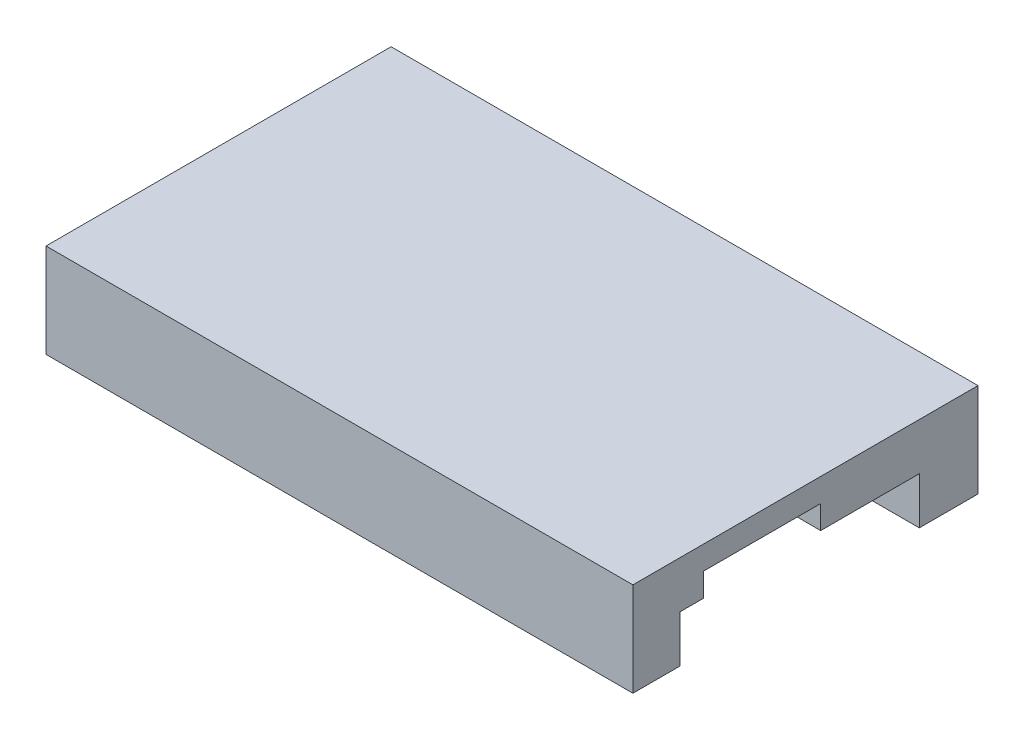
SolidWorks part; units mm, degrees
ref_plane "Front Plane" through (0, 0, 0) normal (0, 0, 1) x (1, 0, 0)
ref_plane "Top Plane" through (0, 0, 0) normal (0, 1, 0) x (1, 0, 0)
ref_plane "Right Plane" through (0, 0, 0) normal (1, 0, 0) x (0, 0, -1)
sketch "Sketch1" plane through (0, 0, 0) normal (0, 1, 0) x (1, 0, 0)
  line L1 (-42.4855, 20.9565) -> (-17.4855, 20.9565)
  line L2 (-42.4855, 20.9565) -> (-42.4855, 6.2565)
  line L3 (-42.4855, 6.2565) -> (-17.4855, 6.2565)
  line L4 (-17.4855, 20.9565) -> (-17.4855, 6.2565)
  dimension "D1" = 25
  dimension "D2" = 14.7
extrude "Boss-Extrude1" add sketch "Sketch1" along normal blind 1
sketch "Sketch2" plane through (0, 1, 0) normal (0, 1, 0) x (1, 0, 0)
  line L0 (-17.4855, 20.9565) -> (-42.4855, 20.9565) construction
  line L1 (-42.4855, 18.2565) -> (-37.4855, 18.2565)
  line L2 (-42.4855, 18.2565) -> (-42.4855, 10.9565)
  line L3 (-42.4855, 10.9565) -> (-37.4855, 10.9565)
  line L4 (-37.4855, 18.2565) -> (-37.4855, 10.9565)
  line L7 (-42.4855, 20.9565) -> (-42.4855, 6.2565) construction
  dimension "D1" = 7.3
  dimension "D2" = 5
  dimension "D3" = 2.7
  dimension "D4" = 0
extrude "Cut-Extrude1" cut sketch "Sketch2" against normal blind 1
sketch "Sketch3" plane through (0, 1, 0) normal (0, 1, 0) x (1, 0, 0)
  line L0 (-17.4855, 6.2565) -> (-17.4855, 20.9565) construction
  line L1 (-17.4855, 14.2565) -> (-24.9855, 14.2565)
  line L2 (-17.4855, 14.2565) -> (-17.4855, 9.2565)
  line L3 (-17.4855, 9.2565) -> (-24.9855, 9.2565)
  line L4 (-24.9855, 14.2565) -> (-24.9855, 9.2565)
  line L5 (-42.4855, 6.2565) -> (-17.4855, 6.2565) construction
  line L6 (-17.4855, 20.9565) -> (-42.4855, 20.9565) construction
  dimension "D1" = 5
  dimension "D2" = 3
  dimension "D3" = 6.7
  dimension "D4" = 7.5
extrude "Cut-Extrude2" cut sketch "Sketch3" against normal blind 1
sketch "Sketch4" plane through (0, 0, 0) normal (0, -1, 0) x (1, 0, 0)
  line L1 (-42.4855, -6.2565) -> (-17.4855, -6.2565)
  line L2 (-42.4855, -6.2565) -> (-42.4855, -7.7565)
  line L3 (-42.4855, -7.7565) -> (-17.4855, -7.7565)
  line L4 (-17.4855, -6.2565) -> (-17.4855, -7.7565)
  line L5 (-42.4855, -20.9565) -> (-42.4855, -18.2565) construction
  line L6 (-17.4855, -6.2565) -> (-20.4855, -6.2565)
  line L7 (-17.4855, -6.2565) -> (-17.4855, -8.2565)
  line L8 (-17.4855, -8.2565) -> (-20.4855, -8.2565)
  line L9 (-20.4855, -6.2565) -> (-20.4855, -8.2565)
  line L10 (-42.4855, -19.4565) -> (-17.4855, -19.4565)
  line L11 (-42.4855, -19.4565) -> (-42.4855, -20.9565)
  line L12 (-42.4855, -20.9565) -> (-17.4855, -20.9565)
  line L13 (-17.4855, -19.4565) -> (-17.4855, -20.9565)
  line L15 (-17.4855, -20.9565) -> (-20.4855, -20.9565)
  line L16 (-17.4855, -20.9565) -> (-17.4855, -18.4565)
  line L17 (-17.4855, -18.4565) -> (-20.4855, -18.4565)
  line L18 (-20.4855, -20.9565) -> (-20.4855, -18.4565)
  line L19 (-17.4855, -6.2565) -> (-17.4855, -9.2565) construction
  line M3 (-17.4855, -9.2565) -> (-17.4855, -6.2565)
  line M5 (-42.4855, -6.2565) -> (-42.4855, -10.9565)
  line M9 (-42.4855, -18.2565) -> (-42.4855, -20.9565)
  line M10 (-42.4855, -20.9565) -> (-17.4855, -20.9565)
  line M11 (-17.4855, -20.9565) -> (-17.4855, -14.2565)
  dimension "D1" = 1.5
  dimension "D2" = 3
  dimension "D3" = 2
  dimension "D4" = 1.5
  dimension "D5" = 2.5
  dimension "D6" = 3
extrude "Boss-Extrude2" add sketch "Sketch4" along normal blind 1 contours L9 L1 L3 M5 | L3 L9 L8 M3 | L18 L10 L17 M11 | L18 L12 L10 M11 | L18 L10 M10 M9
sketch "Sketch9" plane through (0, 1, 0) normal (0, 1, 0) x (1, 0, 0)
  line L1 (-17.4855, 6.2565) -> (-42.4855, 6.2565)
  line L2 (-17.4855, 6.2565) -> (-17.4855, 20.9565)
  line L3 (-17.4855, 20.9565) -> (-42.4855, 20.9565)
  line L4 (-42.4855, 6.2565) -> (-42.4855, 20.9565)
extrude "Boss-Extrude3" add sketch "Sketch9" along normal blind 1
sketch "Sketch11" plane through (0, -1, 0) normal (0, -1, 0) x (-1, 0, 0)
  line L0 (17.4855, 6.2565) -> (17.4855, 8.2565) construction
  line L1 (42.4855, 6.2565) -> (17.4855, 6.2565)
  line L2 (42.4855, 6.2565) -> (42.4855, 7.2565)
  line L3 (42.4855, 7.2565) -> (17.4855, 7.2565)
  line L4 (17.4855, 6.2565) -> (17.4855, 7.2565)
  line L6 (42.4855, 20.9565) -> (17.4855, 20.9565)
  line L7 (42.4855, 20.9565) -> (42.4855, 19.9565)
  line L8 (42.4855, 19.9565) -> (17.4855, 19.9565)
  line L9 (17.4855, 20.9565) -> (17.4855, 19.9565)
  line L10 (17.4855, 8.2565) -> (20.4855, 8.2565) construction
  line L11 (17.4855, 6.2565) -> (19.9855, 6.2565)
  line L12 (17.4855, 6.2565) -> (17.4855, 8.2565)
  line L13 (17.4855, 8.2565) -> (19.9855, 8.2565)
  line L14 (19.9855, 6.2565) -> (19.9855, 8.2565)
  line L15 (17.4855, 18.4565) -> (20.4855, 18.4565) construction
  line L16 (17.4855, 20.9565) -> (19.9855, 20.9565)
  line L17 (17.4855, 20.9565) -> (17.4855, 18.4565)
  line L18 (17.4855, 18.4565) -> (19.9855, 18.4565)
  line L19 (19.9855, 20.9565) -> (19.9855, 18.4565)
  line M3 (20.4855, 8.2565) -> (17.4855, 8.2565)
  line M4 (17.4855, 8.2565) -> (17.4855, 6.2565)
  line M5 (17.4855, 6.2565) -> (42.4855, 6.2565)
  line M6 (42.4855, 6.2565) -> (42.4855, 7.7565)
  dimension "D1" = 1
  dimension "D2" = 1
  dimension "D3" = 2.5
  dimension "D4" = 2.5
extrude "Boss-Extrude5" add sketch "Sketch11" along normal blind 1 contours L14 L1 L3 M6 | L14 L3 M5 M4 | L3 L14 M3 M4 | L19 L8 L17 L18 | L19 L6 L9 L8 | L6 L19 L8 L7
